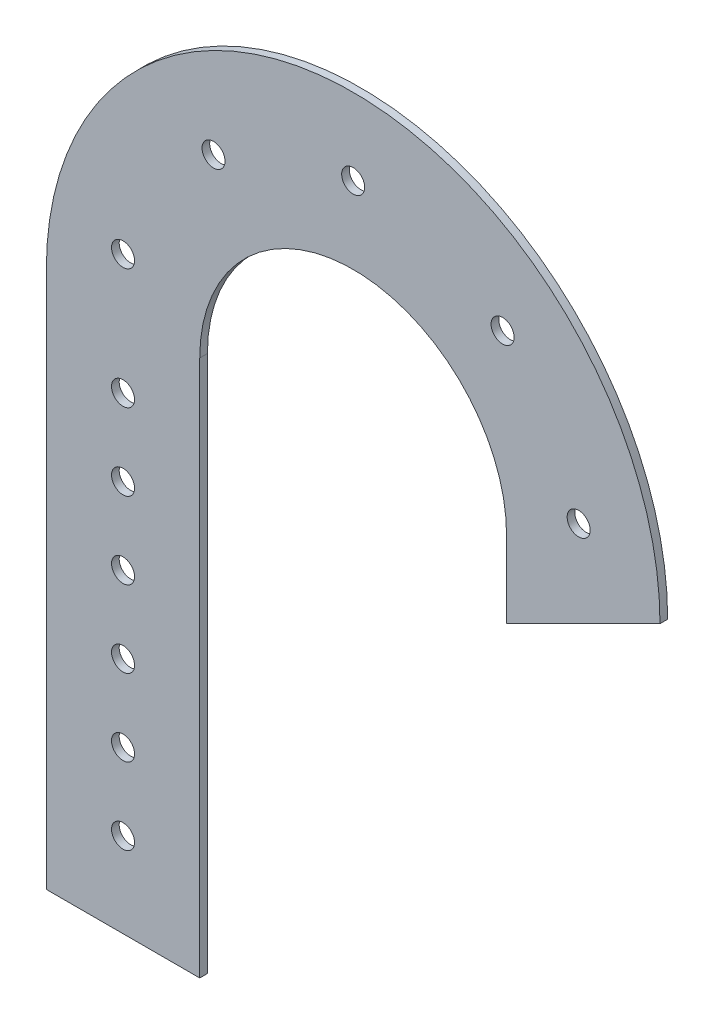
SolidWorks part; units mm, degrees
ref_plane "Front Plane" through (0, 0, 0) normal (0, 0, 1) x (1, 0, 0)
ref_plane "Top Plane" through (0, 0, 0) normal (0, 1, 0) x (1, 0, 0)
ref_plane "Right Plane" through (0, 0, 0) normal (1, 0, 0) x (0, 0, -1)
sketch "Sketch1" plane through (0, 0, 0) normal (0, 0, 1) x (1, 0, 0)
  line L2 (-101.6, 0) -> (-101.6, -177.8)
  line L3 (-50.8, 0) -> (-50.8, -177.8)
  line L4 (-101.6, -177.8) -> (-50.8, -177.8)
  line L14 (50.8, 0) -> (50.8, -25.4)
  line L17 (101.6, 0) -> (50.8, -25.4)
  arc A3 (50.8, 0) -> (-50.8, 0) centre (0, 0) ccw
  arc A4 (101.6, 0) -> (-101.6, 0) centre (0, 0) ccw
  circle A6 centre (0, 76.2) radius 3.81
  circle A8 centre (74.6637, 15.2241) radius 3.81
  circle A9 centre (49.4782, 57.9513) radius 3.81
  circle A10 centre (-46.2344, 60.5708) radius 3.81
  circle A11 centre (-76.2, 17.0811) radius 3.81
  circle A12 centre (-76.2, -22.7482) radius 3.81
  circle A13 centre (-76.2, -48.1482) radius 3.81
  circle A14 centre (-76.2, -73.5482) radius 3.81
  circle A15 centre (-76.2, -98.9482) radius 3.81
  circle A16 centre (-76.2, -124.3482) radius 3.81
  circle A17 centre (-76.2, -149.7482) radius 3.81
  point P18 (101.6, -26.1611)
  point P21 (0, 0)
  point P23 (98.5671, -26.1611)
  point P26 (101.6, -42.1196)
  point P28 (0, 101.6)
  point P30 (0, 0)
  point P32 (50.8, -26.1611)
  point P37 (50.8, -26.1611)
  point P38 (50.8, -26.1611)
  point P39 (98.5671, 24.6389)
  point P40 (0, 0)
  point P41 (101.6, -9.5411)
  point P43 (0, 0)
  point P44 (0, 0)
  point P45 (0, 0)
  point P46 (0, 0)
  dimension "D2" = 50.8
  dimension "D1" = 101.6
  dimension "D3" = 25.4
  dimension "D4" = 76.2
  dimension "D7" = 76.2
  dimension "D5" = 76.2
  dimension "D6" = 76.2
  dimension "D8" = 127
extrude "Boss-Extrude1" add sketch "Sketch1" along normal blind 2.54
